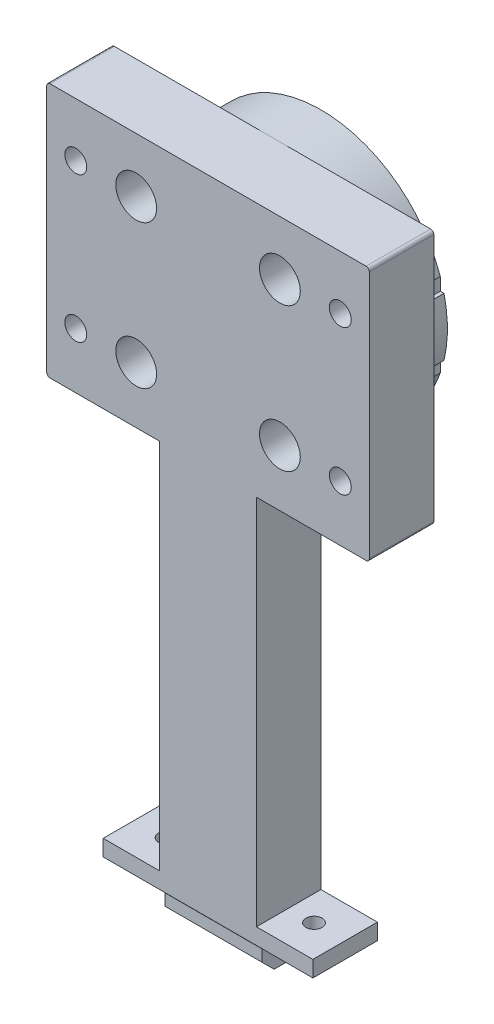
SolidWorks part; units mm, degrees
material "Lega 1060"
ref_plane "Piano frontale" through (0, 0, 0) normal (0, 0, 1) x (1, 0, 0)
ref_plane "Piano superiore" through (0, 0, 0) normal (0, 1, 0) x (1, 0, 0)
ref_plane "Piano destro" through (0, 0, 0) normal (1, 0, 0) x (0, 0, -1)
sketch "Schizzo1" plane through (0, 0, 0) normal (0, 0, 1) x (1, 0, 0)
  arc A6 (-1482, 0) -> (-1488, 0) centre (-1485, 0) ccw
  arc A7 (-1488, 0) -> (-1482, 0) centre (-1485, 0) ccw
  arc A8 (-1475.75, 0) -> (-1444.25, 0) centre (-1460, 0) ccw
  arc A9 (-1444.25, 0) -> (-1475.75, 0) centre (-1460, 0) ccw
extrude "Estrusione-Estrusione2" add sketch "Schizzo1" against normal blind 1
ref_point "Punto1"
sketch "Schizzo2" plane through (0, 0, 0) normal (0, 0, 1) x (1, 0, 0)
  line L4 (-1423, 14.1382) -> (-1423, 18.0858)
  line L5 (-1423, -7.8094) -> (-1423, -3.8618)
  line L6 (-1423, -3.8618) -> (-1421.8471, -3.8618)
  line L7 (-1421.8471, 14.1382) -> (-1423, 14.1382)
  line L8 (-1423, 14.1382) -> (-1423, 18.0858)
  line L9 (-1423, -7.8094) -> (-1423, -3.8618)
  line L10 (-1423, -3.8618) -> (-1421.8471, -3.8618)
  line L11 (-1421.8471, 14.1382) -> (-1423, 14.1382)
  arc A28 (-1437.7261, 30.7356) -> (-1437.7261, 24.0886) centre (-1437.7261, 27.4121) ccw construction
  arc A29 (-1437.7261, 24.0886) -> (-1437.7261, 30.7356) centre (-1437.7261, 27.4121) ccw construction
  arc A30 (-1437.7261, -13.8121) -> (-1437.7261, -20.4591) centre (-1437.7261, -17.1356) ccw construction
  arc A31 (-1437.7261, -20.4591) -> (-1437.7261, -13.8121) centre (-1437.7261, -17.1356) ccw construction
  arc A32 (-1482.2739, -13.8121) -> (-1482.2739, -20.4591) centre (-1482.2739, -17.1356) ccw construction
  arc A33 (-1482.2739, -20.4591) -> (-1482.2739, -13.8121) centre (-1482.2739, -17.1356) ccw construction
  arc A34 (-1482.2739, 30.7356) -> (-1482.2739, 24.0886) centre (-1482.2739, 27.4121) ccw construction
  arc A35 (-1482.2739, 24.0886) -> (-1482.2739, 30.7356) centre (-1482.2739, 27.4121) ccw construction
  arc A36 (-1437.7261, 30.7356) -> (-1437.7261, 24.0886) centre (-1437.7261, 27.4121) ccw
  arc A37 (-1437.7261, 24.0886) -> (-1437.7261, 30.7356) centre (-1437.7261, 27.4121) ccw
  arc A38 (-1437.7261, -13.8121) -> (-1437.7261, -20.4591) centre (-1437.7261, -17.1356) ccw
  arc A39 (-1437.7261, -20.4591) -> (-1437.7261, -13.8121) centre (-1437.7261, -17.1356) ccw
  arc A40 (-1482.2739, -13.8121) -> (-1482.2739, -20.4591) centre (-1482.2739, -17.1356) ccw
  arc A41 (-1482.2739, -20.4591) -> (-1482.2739, -13.8121) centre (-1482.2739, -17.1356) ccw
  arc A42 (-1482.2739, 30.7356) -> (-1482.2739, 24.0886) centre (-1482.2739, 27.4121) ccw
  arc A43 (-1482.2739, 24.0886) -> (-1482.2739, 30.7356) centre (-1482.2739, 27.4121) ccw
  arc A45 (-1421.8471, -3.8618) -> (-1421.8471, 14.1382) centre (-1460, 5.1382) ccw
  arc A46 (-1421.8471, -3.8618) -> (-1421.8471, 14.1382) centre (-1460, 5.1382) ccw
  spline S2 degree 5 poles (565.2025, -110.1054) (-1801.8242, 346.0937) (-1577.0024, -156.9116) (-1394.4658, -79.9681) (-1397.4498, 23.897) (-1450.0442, 43.6583) (-1455.565, 44.6762) (-1466.728, 44.7344) (-1477.2453, 40.9923) (-1482.1201, 38.2081) (-1490.6867, 31.0506) (-1496.3081, 21.4061) (-1498.2363, 16.1337) (-1500.1637, 5.1382) (-1498.2363, -5.8573) (-1496.3081, -11.1296) (-1490.6867, -20.7741) (-1482.1201, -27.9317) (-1477.2453, -30.7159) (-1466.728, -34.4579) (-1455.565, -34.3997) (-1450.0442, -33.3819) (-1397.4498, -13.6205) (-1394.4658, 90.2445) (-1577.0022, 167.1879) (-1801.8238, -335.8164) (565.1978, 120.3809) knots -6.890423 -6.890423 -6.890423 -6.890423 -6.890423 -6.890423 -0.532936 -0.532936 -0.532936 0.168308 0.168308 0.168308 0.869552 0.869552 0.869552 1.570796 1.570796 1.570796 2.27204 2.27204 2.27204 2.973284 2.973284 2.973284 3.674528 3.674528 3.674528 10.032013 10.032013 10.032013 10.032013 10.032013 10.032013 only from (-1423, 18.0858) to (-1423, -7.8094)
  spline S3 degree 5 poles (-1423, 18.0858) (-1424.8159, 23.275) (-1427.5413, 28.146) (-1431.1029, 32.4855) (-1439.5943, 39.732) (-1450.0442, 43.6583) (-1455.565, 44.6762) (-1466.728, 44.7344) (-1477.2453, 40.9923) (-1482.1201, 38.2081) (-1490.6867, 31.0506) (-1496.3081, 21.4061) (-1498.2363, 16.1337) (-1500.1637, 5.1382) (-1498.2363, -5.8573) (-1496.3081, -11.1296) (-1490.6867, -20.7741) (-1482.1201, -27.9317) (-1477.2453, -30.7159) (-1466.728, -34.4579) (-1455.565, -34.3997) (-1450.0442, -33.3819) (-1439.5943, -29.4555) (-1431.1029, -22.209) (-1427.5413, -17.8696) (-1424.8159, -12.9985) (-1423, -7.8094) knots -1.23418 -1.23418 -1.23418 -1.23418 -1.23418 -1.23418 -0.532936 -0.532936 -0.532936 0.168308 0.168308 0.168308 0.869552 0.869552 0.869552 1.570796 1.570796 1.570796 2.27204 2.27204 2.27204 2.973284 2.973284 2.973284 3.674528 3.674528 3.674528 4.375772 4.375772 4.375772 4.375772 4.375772 4.375772
  point P0 (-1423.4633, 13.3696)
  dimension "D1" = 0
extrude "Estrusione-Estrusione3" add sketch "Schizzo2" along normal blind 15
sketch "Schizzo4" plane through (0, 0, 15) normal (0, 0, 1) x (1, 0, 0)
  line L0 (-1460, 0) -> (-1519.7962, 0) construction
  line L5 (-1510, 44.3382) -> (-1410, 44.3382)
  line L6 (-1510, 44.3382) -> (-1510, -34.6618)
  line L7 (-1510, -34.6618) -> (-1410, -34.6618)
  line L8 (-1410, 44.3382) -> (-1410, -34.6618)
  line L9 (-1460, 0) -> (-1460, 38.4815) construction
  spline S0 degree 5 poles (-1423, 18.0858) (-1424.8159, 23.275) (-1427.5413, 28.146) (-1431.1029, 32.4855) (-1439.5943, 39.732) (-1450.0442, 43.6583) (-1455.565, 44.6762) (-1466.728, 44.7344) (-1477.2453, 40.9923) (-1482.1201, 38.2081) (-1490.6867, 31.0506) (-1496.3081, 21.4061) (-1498.2363, 16.1337) (-1500.1637, 5.1382) (-1498.2363, -5.8573) (-1496.3081, -11.1296) (-1490.6867, -20.7741) (-1482.1201, -27.9317) (-1477.2453, -30.7159) (-1466.728, -34.4579) (-1455.565, -34.3997) (-1450.0442, -33.3819) (-1439.5943, -29.4555) (-1431.1029, -22.209) (-1427.5413, -17.8696) (-1424.8159, -12.9985) (-1423, -7.8094) knots -1.23418 -1.23418 -1.23418 -1.23418 -1.23418 -1.23418 -0.532936 -0.532936 -0.532936 0.168308 0.168308 0.168308 0.869552 0.869552 0.869552 1.570796 1.570796 1.570796 2.27204 2.27204 2.27204 2.973284 2.973284 2.973284 3.674528 3.674528 3.674528 4.375772 4.375772 4.375772 4.375772 4.375772 4.375772 construction
  point P4 (0, 0)
  dimension "D1" = 100
  dimension "D2" = 79
extrude "Estrusione-Estrusione4" add sketch "Schizzo4" along normal blind 20
sketch "Schizzo5" plane through (0, 0, -1) normal (0, 0, -1) x (-1, 0, 0)
  arc A11 (1437.7261, -13.8121) -> (1437.7261, -20.4591) centre (1437.7261, -17.1356) ccw construction
  arc A12 (1437.7261, -20.4591) -> (1437.7261, -13.8121) centre (1437.7261, -17.1356) ccw construction
  arc A13 (1437.7261, 24.0886) -> (1437.7261, 30.7356) centre (1437.7261, 27.4121) ccw construction
  arc A14 (1437.7261, 30.7356) -> (1437.7261, 24.0886) centre (1437.7261, 27.4121) ccw construction
  arc A15 (1482.2739, 24.0886) -> (1482.2739, 30.7356) centre (1482.2739, 27.4121) ccw construction
  arc A16 (1482.2739, 30.7356) -> (1482.2739, 24.0886) centre (1482.2739, 27.4121) ccw construction
  arc A17 (1482.2739, -20.4591) -> (1482.2739, -13.8121) centre (1482.2739, -17.1356) ccw construction
  arc A18 (1482.2739, -13.8121) -> (1482.2739, -20.4591) centre (1482.2739, -17.1356) ccw construction
  arc A19 (1437.7261, -13.8121) -> (1437.7261, -20.4591) centre (1437.7261, -17.1356) ccw
  arc A20 (1437.7261, -20.4591) -> (1437.7261, -13.8121) centre (1437.7261, -17.1356) ccw
  arc A21 (1437.7261, 24.0886) -> (1437.7261, 30.7356) centre (1437.7261, 27.4121) ccw
  arc A22 (1437.7261, 30.7356) -> (1437.7261, 24.0886) centre (1437.7261, 27.4121) ccw
  arc A23 (1482.2739, 24.0886) -> (1482.2739, 30.7356) centre (1482.2739, 27.4121) ccw
  arc A24 (1482.2739, 30.7356) -> (1482.2739, 24.0886) centre (1482.2739, 27.4121) ccw
  arc A25 (1482.2739, -20.4591) -> (1482.2739, -13.8121) centre (1482.2739, -17.1356) ccw
  arc A26 (1482.2739, -13.8121) -> (1482.2739, -20.4591) centre (1482.2739, -17.1356) ccw
extrude "Taglio-Estrusione2" cut sketch "Schizzo5" against normal up to surface (36 mm away) up to face at (-1460, 4.8382, 35)
fillet "Raccordo1" radius 1 4 edges at (-1510, -34.6618, 25) (-1510, 44.3382, 25) (-1410, -34.6618, 25) (-1410, 44.3382, 25)
sketch "Schizzo8" plane through (0, 0, 35) normal (0, 0, 1) x (1, 0, 0)
  line L0 (-1509, -34.6618) -> (-1411, -34.6618) construction
  line L1 (-1460, -34.6618) -> (-1475, -34.6618)
  line L3 (-1465.76, -155) -> (-1475, -155)
  line L4 (-1475, -34.6618) -> (-1475, -155)
  line L6 (-1460, -34.6618) -> (-1445, -34.6618)
  line L8 (-1465.76, -155) -> (-1445, -155)
  line L9 (-1445, -34.6618) -> (-1445, -155)
  dimension "D1" = 15
  dimension "D2" = 15
extrude "Estrusione-Estrusione5" add sketch "Schizzo8" against normal up to surface (20 mm away) up to face at (-1442.8532, 10.4507, 15)
ref_plane "Piano1" through (0, 0, 25) normal (0, 0, -1) x (-1, 0, 0)
sketch "Schizzo10" plane through (-1475, 0, 0) normal (-1, 0, 0) x (0, 0, 1)
  line L0 (20.7, -155) -> (20.7, -156.76)
  line L1 (15, -155) -> (35, -155) construction
  line L2 (20.7, -156.76) -> (16.7, -156.76)
  line L3 (16.7, -156.76) -> (16.7, -160.36)
  line L7 (33.3, -160.36) -> (33.3, -156.76)
  line L8 (33.3, -156.76) -> (29.3, -156.76)
  line L9 (29.3, -156.76) -> (29.3, -155)
  line L10 (38, -155) -> (12, -155) construction
  line L11 (29.3, -155) -> (20.7, -155)
  line L12 (35, -34.6618) -> (35, -155) construction
  line L13 (15, -155) -> (15, -34.6618) construction
  line L14 (16.7, -160.36) -> (20.483, -164.143)
  line L15 (20.483, -164.143) -> (29.517, -164.143)
  line L16 (29.517, -164.143) -> (33.3, -160.36)
  dimension "D1" = 5.7
  dimension "D2" = 1.76
  dimension "D3" = 5.7
  dimension "D4" = 4
  dimension "D5" = 4
  dimension "D6" = 5.35
  dimension "D7" = 3.6
  dimension "D8" = 3.6
  dimension "D9" = 1.76
  dimension "D10" = 5.35
  dimension "D11" = 9.034
extrude "Estrusione-Estrusione6" add sketch "Schizzo10" against normal up to surface (30 mm away) up to face at (-1445, -94.8309, 25)
sketch "Schizzo11" plane through (-1445, 0, 0) normal (1, 0, 0) x (0, 0, -1)
  line L0 (-15, -34.6618) -> (-15, -155) construction
  line L1 (-35, -155) -> (-15, -155)
  line L2 (-35, -155) -> (-35, -150)
  line L3 (-35, -150) -> (-15, -150)
  line L4 (-15, -155) -> (-15, -150)
  dimension "D1" = 5
extrude "Estrusione-Estrusione7" add sketch "Schizzo11" along normal blind 17.5 and the other way blind 47.5
sketch "Schizzo13" plane through (0, -155, 0) normal (0, -1, 0) x (1, 0, 0)
  circle A0 centre (-1437.15, 25) radius 2.5 construction
  circle A1 centre (-1482.85, 25) radius 2.5 construction
  circle A2 centre (-1437.15, 25) radius 2.5
  circle A3 centre (-1482.85, 25) radius 2.5
extrude "Taglio-Estrusione5" cut sketch "Schizzo13" against normal up to next
sketch "Schizzo14" plane through (0, 0, 35) normal (0, 0, 1) x (1, 0, 0)
  circle A0 centre (-1437.7261, -17.1356) radius 3.3235 construction
  circle A1 centre (-1482.2739, -17.1356) radius 3.3235 construction
  circle A2 centre (-1437.7261, 27.4121) radius 3.3235 construction
  circle A3 centre (-1482.2739, 27.4121) radius 3.3235 construction
  circle A4 centre (-1437.7261, -17.1356) radius 3.3235
  circle A5 centre (-1482.2739, -17.1356) radius 3.3235
  circle A6 centre (-1437.7261, 27.4121) radius 3.3235
  circle A7 centre (-1482.2739, 27.4121) radius 3.3235
  circle A8 centre (-1482.2739, 27.4121) radius 6.3235
  circle A9 centre (-1482.2739, -17.1356) radius 6.3235
  circle A10 centre (-1437.7261, -17.1356) radius 6.3235
  circle A11 centre (-1437.7261, 27.4121) radius 6.3235
  dimension "D1" = 3
extrude "Taglio-Estrusione6" cut sketch "Schizzo14" against normal blind 10
sketch "Schizzo15" plane through (0, 0, 35) normal (0, 0, 1) x (1, 0, 0)
  arc A0 (-1419, 24.2382) -> (-1419, 31.0382) centre (-1419, 27.6382) ccw construction
  arc A1 (-1419, 31.0382) -> (-1419, 24.2382) centre (-1419, 27.6382) ccw construction
  arc A2 (-1419, -13.9618) -> (-1419, -20.7618) centre (-1419, -17.3618) ccw construction
  arc A3 (-1419, -20.7618) -> (-1419, -13.9618) centre (-1419, -17.3618) ccw construction
  arc A4 (-1501, -13.9618) -> (-1501, -20.7618) centre (-1501, -17.3618) ccw construction
  arc A5 (-1501, -20.7618) -> (-1501, -13.9618) centre (-1501, -17.3618) ccw construction
  arc A6 (-1501, 31.0382) -> (-1501, 24.2382) centre (-1501, 27.6382) ccw construction
  arc A7 (-1501, 24.2382) -> (-1501, 31.0382) centre (-1501, 27.6382) ccw construction
  arc A8 (-1419, 24.2382) -> (-1419, 31.0382) centre (-1419, 27.6382) ccw
  arc A9 (-1419, 31.0382) -> (-1419, 24.2382) centre (-1419, 27.6382) ccw
  arc A10 (-1419, -13.9618) -> (-1419, -20.7618) centre (-1419, -17.3618) ccw
  arc A11 (-1419, -20.7618) -> (-1419, -13.9618) centre (-1419, -17.3618) ccw
  arc A12 (-1501, -13.9618) -> (-1501, -20.7618) centre (-1501, -17.3618) ccw
  arc A13 (-1501, -20.7618) -> (-1501, -13.9618) centre (-1501, -17.3618) ccw
  arc A14 (-1501, 31.0382) -> (-1501, 24.2382) centre (-1501, 27.6382) ccw
  arc A15 (-1501, 24.2382) -> (-1501, 31.0382) centre (-1501, 27.6382) ccw
extrude "Taglio-Estrusione7" cut sketch "Schizzo15" against normal up to surface (20 mm away)
sketch "Schizzo7" plane through (0, 0, 15) normal (0, 0, -1) x (-1, 0, 0)
  circle A0 centre (1419, -17.3618) radius 3.4 construction
  circle A2 centre (1419, 27.6382) radius 6
  circle A3 centre (1501, -17.3618) radius 6
  circle A4 centre (1501, 27.6382) radius 6
  circle A5 centre (1419, -17.3618) radius 6
  point P8 (1419, -27.6382)
  point P11 (1501, -27.6382)
  point P12 (1501, -17.3618)
  dimension "D1" = 12
extrude "Taglio-Estrusione4" cut sketch "Schizzo7" against normal blind 8
